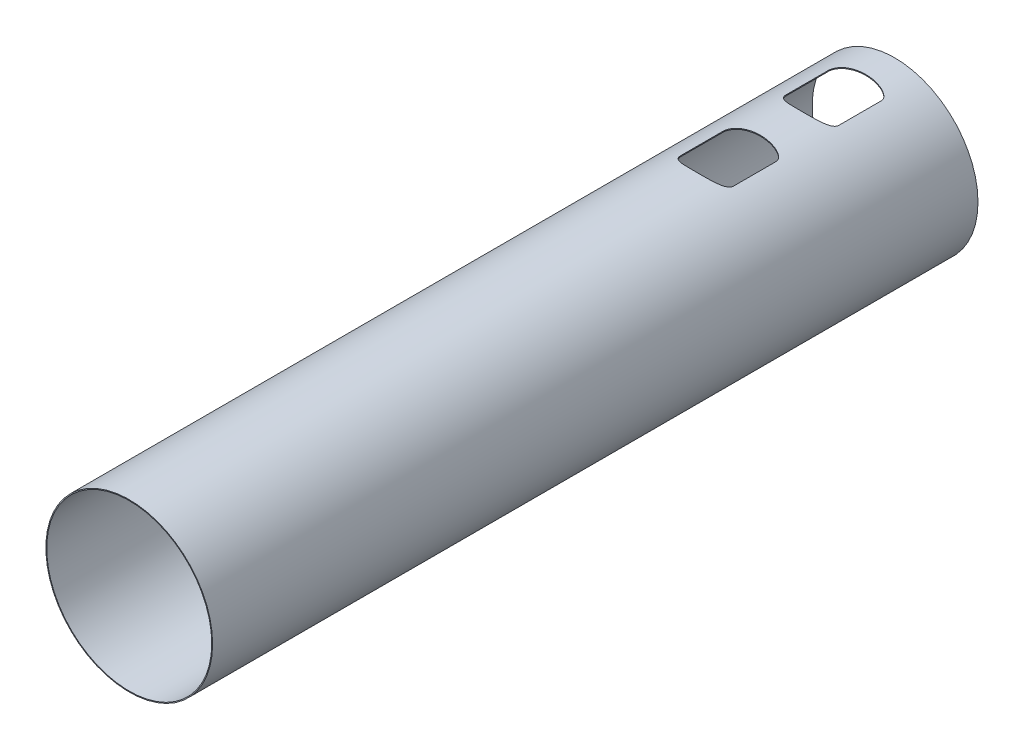
SolidWorks part; units mm, degrees
material "Hexcel AS4C (3000 Filaments)"
ref_plane "Front" through (0, 0, 0) normal (0, 0, 1) x (1, 0, 0)
ref_plane "Top" through (0, 0, 0) normal (0, 1, 0) x (1, 0, 0)
ref_plane "Right" through (0, 0, 0) normal (1, 0, 0) x (0, 0, -1)
sketch "Sketch1" plane through (0, 0, 0) normal (0, 0, 1) x (1, 0, 0)
  circle A0 centre (0, 0) radius 117.5
  circle A1 centre (0, 0) radius 118.75
  dimension "D1" = 1.25
  dimension "D2" = 237.5
extrude "Extrude1" add sketch "Sketch1" along normal blind 540 and the other way blind 550
sketch "Sketch2" plane through (0, 0, 0) normal (0, 1, 0) x (1, 0, 0)
  line L10 (-37.6075, 493.5437) -> (-37.6075, 432.8563)
  line L11 (37.6075, 432.8563) -> (37.6075, 493.5437)
  line L16 (-37.6075, 343.5437) -> (-37.6075, 282.8563)
  line L17 (37.6075, 282.8563) -> (37.6075, 343.5437)
  spline S31 degree 3 poles (23.3224, 505.9891) (21.4279, 506.5379) (19.5118, 506.9706) (15.6505, 507.6799) (13.7051, 507.9553) (9.7917, 508.385) (7.8302, 508.5381) (3.9039, 508.7401) (1.9383, 508.789) (-1.9977, 508.788) (-3.9629, 508.738) (-7.8776, 508.5347) (-9.8286, 508.3814) (-13.7156, 507.9537) (-15.6516, 507.6795) (-19.504, 506.9721) (-21.4206, 506.54) (-23.3224, 505.9891) knots 0 0 0 0 0.125 0.125 0.25 0.25 0.375 0.375 0.5 0.5 0.625 0.625 0.75 0.75 0.875 0.875 1 1 1 1
  spline S32 degree 3 poles (-23.3224, 505.9891) (-24.9458, 505.5189) (-26.54, 504.9679) (-28.8644, 503.9567) (-29.6245, 503.5894) (-31.0942, 502.7867) (-31.8056, 502.3504) (-33.1678, 501.3873) (-33.8188, 500.8608) (-34.732, 499.9767) (-35.0266, 499.6643) (-35.5763, 499.016) (-35.8332, 498.679) (-36.3061, 497.9757) (-36.5223, 497.6082) (-36.9039, 496.8421) (-37.0661, 496.4507) (-37.3308, 495.6502) (-37.4331, 495.2411) (-37.5717, 494.4036) (-37.6075, 493.9732) (-37.6075, 493.5437) knots 0 0 0 0 0.25 0.25 0.375 0.375 0.5 0.5 0.625 0.625 0.6875 0.6875 0.75 0.75 0.8125 0.8125 0.875 0.875 0.9375 0.9375 1 1 1 1
  spline S33 degree 3 poles (-37.6075, 432.8563) (-37.6075, 432.0004) (-37.4683, 431.1695) (-37.0694, 429.9573) (-36.9054, 429.5618) (-36.5289, 428.8041) (-36.3153, 428.4392) (-35.8428, 427.734) (-35.5834, 427.3931) (-35.037, 426.7472) (-34.7484, 426.4404) (-33.8436, 425.561) (-33.1889, 425.0282) (-31.8019, 424.0465) (-31.0835, 423.6069) (-29.6099, 422.8032) (-28.8547, 422.4389) (-26.5461, 421.435) (-24.9459, 420.8811) (-23.3224, 420.4109) knots 0 0 0 0 0.125 0.125 0.1875 0.1875 0.25 0.25 0.3125 0.3125 0.375 0.375 0.5 0.5 0.625 0.625 0.75 0.75 1 1 1 1
  spline S34 degree 3 poles (-23.3224, 420.4109) (-21.4279, 419.8621) (-19.5118, 419.4294) (-15.6505, 418.7202) (-13.7051, 418.4446) (-9.7917, 418.015) (-7.8302, 417.8619) (-3.9039, 417.6599) (-1.9383, 417.611) (1.9977, 417.612) (3.9629, 417.662) (7.8776, 417.8653) (9.8286, 418.0186) (13.7155, 418.4463) (15.6516, 418.7204) (19.504, 419.4279) (21.4206, 419.86) (23.3224, 420.4109) knots 0 0 0 0 0.125 0.125 0.25 0.25 0.375 0.375 0.5 0.5 0.625 0.625 0.75 0.75 0.875 0.875 1 1 1 1
  spline S35 degree 3 poles (23.3224, 420.4109) (24.9461, 420.8812) (26.5401, 421.4322) (28.8631, 422.4427) (29.626, 422.8112) (31.1023, 423.618) (31.8177, 424.0571) (32.8466, 424.7859) (33.182, 425.0408) (33.8352, 425.5784) (34.1534, 425.8617) (35.0616, 426.7466) (35.6109, 427.3864) (36.5565, 428.8017) (36.9352, 429.5527) (37.3307, 430.7503) (37.4342, 431.1651) (37.5723, 432.0054) (37.6075, 432.429) (37.6075, 432.8563) knots 0 0 0 0 0.25 0.25 0.375 0.375 0.5 0.5 0.5625 0.5625 0.625 0.625 0.75 0.75 0.875 0.875 0.9375 0.9375 1 1 1 1
  spline S36 degree 3 poles (37.6075, 493.5437) (37.6075, 494.3996) (37.4679, 495.2306) (37.0693, 496.4431) (36.9051, 496.8384) (36.5283, 497.5958) (36.3147, 497.9609) (35.8425, 498.6664) (35.5831, 499.0072) (35.0367, 499.6527) (34.7481, 499.9594) (33.8437, 500.839) (33.1887, 501.3723) (31.802, 502.3534) (31.0837, 502.793) (29.6102, 503.5967) (28.8551, 503.9609) (26.5463, 504.9649) (24.9459, 505.5189) (23.3224, 505.9891) knots 0 0 0 0 0.125 0.125 0.1875 0.1875 0.25 0.25 0.3125 0.3125 0.375 0.375 0.5 0.5 0.625 0.625 0.75 0.75 1 1 1 1
  spline S49 degree 3 poles (23.3224, 355.9891) (21.4279, 356.5379) (19.5118, 356.9706) (15.6505, 357.6799) (13.7051, 357.9553) (9.7917, 358.385) (7.8302, 358.5381) (3.9039, 358.7401) (1.9383, 358.789) (-1.9977, 358.788) (-3.9629, 358.738) (-7.8776, 358.5347) (-9.8286, 358.3814) (-13.7156, 357.9537) (-15.6516, 357.6795) (-19.504, 356.9721) (-21.4206, 356.54) (-23.3224, 355.9891) knots 0 0 0 0 0.125 0.125 0.25 0.25 0.375 0.375 0.5 0.5 0.625 0.625 0.75 0.75 0.875 0.875 1 1 1 1
  spline S50 degree 3 poles (-23.3224, 355.9891) (-24.9458, 355.5189) (-26.54, 354.9679) (-28.8644, 353.9567) (-29.6245, 353.5894) (-31.0942, 352.7867) (-31.8056, 352.3504) (-33.1678, 351.3873) (-33.8188, 350.8608) (-34.732, 349.9767) (-35.0266, 349.6643) (-35.5763, 349.016) (-35.8332, 348.679) (-36.3061, 347.9757) (-36.5223, 347.6082) (-36.9039, 346.8421) (-37.0661, 346.4507) (-37.3308, 345.6502) (-37.4331, 345.2411) (-37.5717, 344.4036) (-37.6075, 343.9732) (-37.6075, 343.5437) knots 0 0 0 0 0.25 0.25 0.375 0.375 0.5 0.5 0.625 0.625 0.6875 0.6875 0.75 0.75 0.8125 0.8125 0.875 0.875 0.9375 0.9375 1 1 1 1
  spline S51 degree 3 poles (-37.6075, 282.8563) (-37.6075, 282.0004) (-37.4683, 281.1695) (-37.0694, 279.9573) (-36.9054, 279.5618) (-36.5289, 278.8041) (-36.3153, 278.4392) (-35.8428, 277.734) (-35.5834, 277.3931) (-35.037, 276.7472) (-34.7484, 276.4404) (-33.8436, 275.561) (-33.1889, 275.0282) (-31.8019, 274.0465) (-31.0835, 273.6069) (-29.6099, 272.8032) (-28.8547, 272.4389) (-26.5461, 271.435) (-24.9459, 270.8811) (-23.3224, 270.4109) knots 0 0 0 0 0.125 0.125 0.1875 0.1875 0.25 0.25 0.3125 0.3125 0.375 0.375 0.5 0.5 0.625 0.625 0.75 0.75 1 1 1 1
  spline S52 degree 3 poles (-23.3224, 270.4109) (-21.4279, 269.8621) (-19.5118, 269.4294) (-15.6505, 268.7202) (-13.7051, 268.4446) (-9.7917, 268.015) (-7.8302, 267.8619) (-3.9039, 267.6599) (-1.9383, 267.611) (1.9977, 267.612) (3.9629, 267.662) (7.8776, 267.8653) (9.8286, 268.0186) (13.7155, 268.4463) (15.6516, 268.7204) (19.504, 269.4279) (21.4206, 269.86) (23.3224, 270.4109) knots 0 0 0 0 0.125 0.125 0.25 0.25 0.375 0.375 0.5 0.5 0.625 0.625 0.75 0.75 0.875 0.875 1 1 1 1
  spline S53 degree 3 poles (23.3224, 270.4109) (24.9461, 270.8812) (26.5401, 271.4322) (28.8631, 272.4427) (29.626, 272.8112) (31.1023, 273.618) (31.8177, 274.0571) (32.8466, 274.7859) (33.182, 275.0408) (33.8352, 275.5784) (34.1534, 275.8617) (35.0616, 276.7466) (35.6109, 277.3864) (36.5565, 278.8017) (36.9352, 279.5527) (37.3307, 280.7503) (37.4342, 281.1651) (37.5723, 282.0054) (37.6075, 282.429) (37.6075, 282.8563) knots 0 0 0 0 0.25 0.25 0.375 0.375 0.5 0.5 0.5625 0.5625 0.625 0.625 0.75 0.75 0.875 0.875 0.9375 0.9375 1 1 1 1
  spline S54 degree 3 poles (37.6075, 343.5437) (37.6075, 344.3996) (37.4679, 345.2306) (37.0693, 346.4431) (36.9051, 346.8384) (36.5283, 347.5958) (36.3147, 347.9609) (35.8425, 348.6664) (35.5831, 349.0072) (35.0367, 349.6527) (34.7481, 349.9594) (33.8437, 350.839) (33.1887, 351.3723) (31.802, 352.3534) (31.0837, 352.793) (29.6102, 353.5967) (28.8551, 353.9609) (26.5463, 354.9649) (24.9459, 355.5189) (23.3224, 355.9891) knots 0 0 0 0 0.125 0.125 0.1875 0.1875 0.25 0.25 0.3125 0.3125 0.375 0.375 0.5 0.5 0.625 0.625 0.75 0.75 1 1 1 1
extrude "Extrude2" cut sketch "Sketch2" along normal through all
sketch "Sketch3" plane through (0, 0, 0) normal (0, 1, 0) x (1, 0, 0)
  line L8 (37.6075, 357.8563) -> (37.6075, 418.5437)
  line L9 (-37.6075, 418.5437) -> (-37.6075, 357.8563)
  spline S24 degree 3 poles (23.3224, 345.4109) (24.9458, 345.8811) (26.54, 346.4321) (28.8644, 347.4433) (29.6245, 347.8106) (31.0942, 348.6133) (31.8056, 349.0496) (33.1678, 350.0127) (33.8188, 350.5392) (34.732, 351.4233) (35.0266, 351.7357) (35.5763, 352.384) (35.8332, 352.721) (36.3061, 353.4243) (36.5223, 353.7918) (36.9039, 354.5579) (37.0661, 354.9493) (37.3308, 355.7498) (37.4331, 356.1589) (37.5717, 356.9964) (37.6075, 357.4268) (37.6075, 357.8563) knots 0 0 0 0 0.25 0.25 0.375 0.375 0.5 0.5 0.625 0.625 0.6875 0.6875 0.75 0.75 0.8125 0.8125 0.875 0.875 0.9375 0.9375 1 1 1 1
  spline S25 degree 3 poles (-23.3224, 345.4109) (-21.4279, 344.8621) (-19.5118, 344.4294) (-15.6505, 343.7201) (-13.7051, 343.4447) (-9.7917, 343.015) (-7.8302, 342.8619) (-3.9039, 342.6599) (-1.9383, 342.611) (1.9977, 342.612) (3.9629, 342.662) (7.8776, 342.8653) (9.8286, 343.0186) (13.7156, 343.4463) (15.6516, 343.7205) (19.504, 344.4279) (21.4206, 344.86) (23.3224, 345.4109) knots 0 0 0 0 0.125 0.125 0.25 0.25 0.375 0.375 0.5 0.5 0.625 0.625 0.75 0.75 0.875 0.875 1 1 1 1
  spline S26 degree 3 poles (-37.6075, 357.8563) (-37.6075, 357.0004) (-37.4679, 356.1694) (-37.0693, 354.9569) (-36.9051, 354.5616) (-36.5283, 353.8042) (-36.3147, 353.4391) (-35.8425, 352.7336) (-35.5831, 352.3928) (-35.0367, 351.7473) (-34.7481, 351.4406) (-33.8437, 350.561) (-33.1887, 350.0277) (-31.802, 349.0466) (-31.0837, 348.607) (-29.6102, 347.8033) (-28.8551, 347.4391) (-26.5463, 346.4351) (-24.9459, 345.8811) (-23.3224, 345.4109) knots 0 0 0 0 0.125 0.125 0.1875 0.1875 0.25 0.25 0.3125 0.3125 0.375 0.375 0.5 0.5 0.625 0.625 0.75 0.75 1 1 1 1
  spline S27 degree 3 poles (-23.3224, 430.9891) (-24.9461, 430.5188) (-26.5401, 429.9678) (-28.8631, 428.9573) (-29.626, 428.5888) (-31.1023, 427.782) (-31.8177, 427.3429) (-32.8466, 426.6141) (-33.182, 426.3592) (-33.8352, 425.8216) (-34.1534, 425.5383) (-35.0616, 424.6534) (-35.6109, 424.0136) (-36.5565, 422.5983) (-36.9352, 421.8473) (-37.3307, 420.6497) (-37.4342, 420.2349) (-37.5723, 419.3946) (-37.6075, 418.971) (-37.6075, 418.5437) knots 0 0 0 0 0.25 0.25 0.375 0.375 0.5 0.5 0.5625 0.5625 0.625 0.625 0.75 0.75 0.875 0.875 0.9375 0.9375 1 1 1 1
  spline S28 degree 3 poles (23.3224, 430.9891) (21.4279, 431.5379) (19.5118, 431.9706) (15.6505, 432.6798) (13.7051, 432.9554) (9.7917, 433.385) (7.8302, 433.5381) (3.9039, 433.7401) (1.9383, 433.789) (-1.9977, 433.788) (-3.9629, 433.738) (-7.8776, 433.5347) (-9.8286, 433.3814) (-13.7155, 432.9537) (-15.6516, 432.6796) (-19.504, 431.9721) (-21.4206, 431.54) (-23.3224, 430.9891) knots 0 0 0 0 0.125 0.125 0.25 0.25 0.375 0.375 0.5 0.5 0.625 0.625 0.75 0.75 0.875 0.875 1 1 1 1
  spline S29 degree 3 poles (37.6075, 418.5437) (37.6075, 419.3996) (37.4683, 420.2305) (37.0694, 421.4427) (36.9054, 421.8382) (36.5289, 422.5959) (36.3153, 422.9608) (35.8428, 423.666) (35.5834, 424.0069) (35.037, 424.6528) (34.7484, 424.9596) (33.8436, 425.839) (33.1889, 426.3718) (31.8019, 427.3535) (31.0835, 427.7931) (29.6099, 428.5968) (28.8547, 428.9611) (26.5461, 429.965) (24.9459, 430.5189) (23.3224, 430.9891) knots 0 0 0 0 0.125 0.125 0.1875 0.1875 0.25 0.25 0.3125 0.3125 0.375 0.375 0.5 0.5 0.625 0.625 0.75 0.75 1 1 1 1
extrude "Extrude3" cut sketch "Sketch3" against normal blind 183
ref_plane "IP" through (0, 0, -7.2) normal (0, 0, 1) x (1, 0, 0)
sketch "Sketch4" [suppressed] plane through (0, 0, 540) normal (0, 0, 1) x (1, 0, 0)
  circle A0 centre (0, 0) radius 118.75 construction
  circle A1 centre (0, 0) radius 118.75
extrude "Cut-Extrude1" [suppressed] cut sketch "Sketch4" against normal up to vertex
